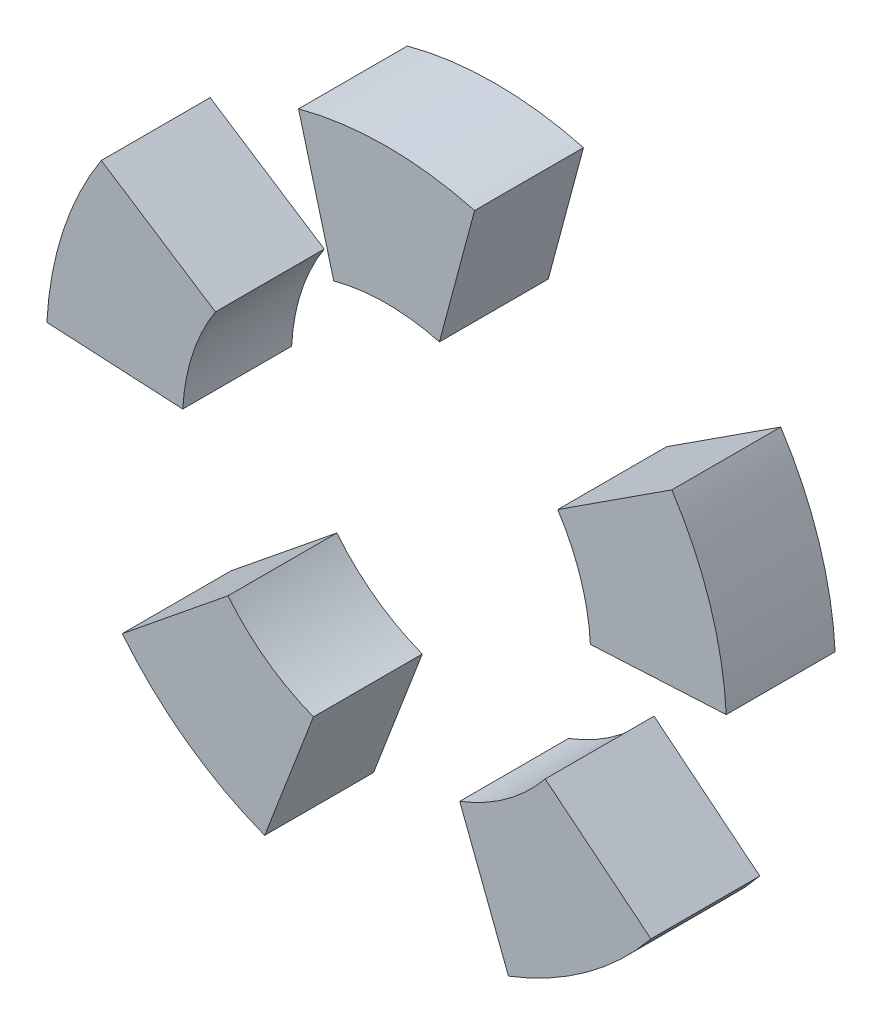
SolidWorks part; units mm, degrees
ref_plane "Front Plane" through (0, 0, 0) normal (0, 0, 1) x (1, 0, 0)
ref_plane "Top Plane" through (0, 0, 0) normal (0, 1, 0) x (1, 0, 0)
ref_plane "Right Plane" through (0, 0, 0) normal (1, 0, 0) x (0, 0, -1)
sketch "Sketch1" plane through (0, 0, 0) normal (0, 0, 1) x (1, 0, 0)
  line L0 (-3.8823, 14.4889) -> (-6.4705, 24.1481)
  line L1 (3.8823, 14.4889) -> (6.4705, 24.1481)
  line L2 (0, 0) -> (0, 27.2948) construction
  line L3 (12.5801, 8.1696) -> (20.9668, 13.616)
  line L4 (14.9794, 0.785) -> (24.9657, 1.3084)
  line L5 (11.6572, -9.4398) -> (19.4286, -15.733)
  line L6 (5.3755, -14.0037) -> (8.9592, -23.3395)
  line L7 (-5.3755, -14.0037) -> (-8.9592, -23.3395)
  line L8 (-11.6572, -9.4398) -> (-19.4286, -15.733)
  line L9 (-14.9794, 0.785) -> (-24.9657, 1.3084)
  line L10 (-12.5801, 8.1696) -> (-20.9668, 13.616)
  arc A0 (-12.5801, 8.1696) -> (-14.9794, 0.785) centre (0, 0) ccw
  arc A1 (-20.9668, 13.616) -> (-24.9657, 1.3084) centre (0, 0) ccw
  circle A2 centre (0, 0) radius 15 construction
  arc A3 (3.8823, 14.4889) -> (-3.8823, 14.4889) centre (0, 0) ccw
  arc A4 (14.9794, 0.785) -> (12.5801, 8.1696) centre (0, 0) ccw
  arc A5 (5.3755, -14.0037) -> (11.6572, -9.4398) centre (0, 0) ccw
  arc A6 (-11.6572, -9.4398) -> (-5.3755, -14.0037) centre (0, 0) ccw
  circle A7 centre (0, 0) radius 25 construction
  arc A8 (-19.4286, -15.733) -> (-8.9592, -23.3395) centre (0, 0) ccw
  arc A9 (8.9592, -23.3395) -> (19.4286, -15.733) centre (0, 0) ccw
  arc A10 (24.9657, 1.3084) -> (20.9668, 13.616) centre (0, 0) ccw
  arc A11 (6.4705, 24.1481) -> (-6.4705, 24.1481) centre (0, 0) ccw
  point P18 (0, 0)
  dimension "D1" = 30
  dimension "D3" = 15
  dimension "D4" = 15
  dimension "D2" = 10
  dimension "D5" = 5
extrude "Boss-Extrude1" add sketch "Sketch1" along normal blind 8
